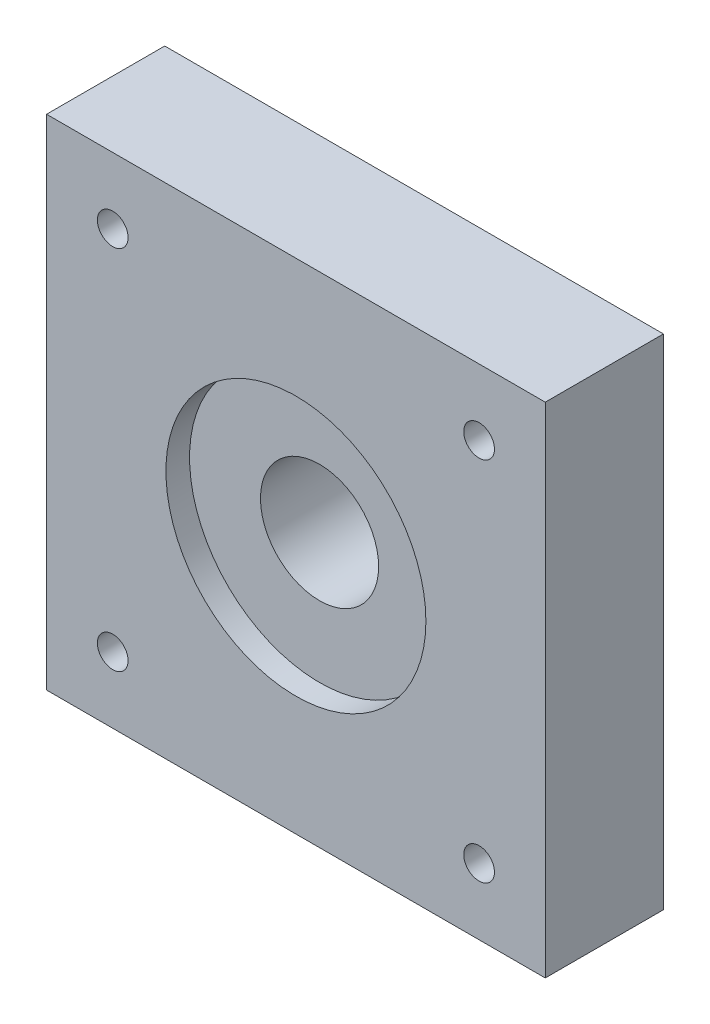
SolidWorks part; units mm, degrees
ref_plane "Front" through (0, 0, 0) normal (0, 0, 1) x (1, 0, 0)
ref_plane "Top" through (0, 0, 0) normal (0, 1, 0) x (1, 0, 0)
ref_plane "Right" through (0, 0, 0) normal (1, 0, 0) x (0, 0, -1)
sketch "草图1" plane through (0, 0, 0) normal (0, 0, 1) x (1, 0, 0)
  line L1 (-21.1, -21.1) -> (21.1, -21.1)
  line L2 (-21.1, -21.1) -> (-21.1, 21.1)
  line L3 (-21.1, 21.1) -> (21.1, 21.1)
  line L4 (21.1, -21.1) -> (21.1, 21.1)
  line L5 (-21.1, -21.1) -> (21.1, 21.1) construction
  line L6 (-21.1, 21.1) -> (21.1, -21.1) construction
  point P0 (0, 0)
  point P6 (11.6426, -11.7023)
  dimension "D2" = 42.2
extrude "凸台-拉伸1" add sketch "草图1" along normal blind 10
sketch "草图2" plane through (0, 0, 0) normal (0, 0, -1) x (-1, 0, 0)
  line L5 (-12.5, 0) -> (12.5, 0) construction
  line L6 (0, -12.5) -> (0, 12.5) construction
  circle A0 centre (12.5, 0) radius 1.6
  circle A1 centre (0, -12.5) radius 1.6
  circle A2 centre (-12.5, 0) radius 1.6
  circle A3 centre (0, 12.5) radius 1.6
  circle A4 centre (-15.5, 15.5) radius 3
  circle A5 centre (15.5, 15.5) radius 3
  circle A6 centre (15.5, -15.5) radius 3
  circle A7 centre (-15.5, -15.5) radius 3
  point P0 (0, 0)
  point P10 (0, 0)
  point P13 (0, 0)
  point P16 (0, 0)
  point P19 (0, 0)
  point P27 (0, 0)
  dimension "D2" = 3.2
  dimension "D1" = 25
  dimension "D4" = 4
  dimension "D3" = 4
extrude "切除-拉伸1" cut sketch "草图2" against normal blind 6
sketch "草图3" plane through (0, 0, 10) normal (0, 0, 1) x (1, 0, 0)
  circle A0 centre (0, 0) radius 11
extrude "切除-拉伸2" cut sketch "草图3" against normal blind 2
sketch "草图4" plane through (0, 0, 0) normal (0, 0, -1) x (-1, 0, 0)
  circle A0 centre (0, 0) radius 5
extrude "切除-拉伸3" cut sketch "草图4" against normal through all
sketch "草图5" plane through (0, 0, 10) normal (0, 0, 1) x (1, 0, 0)
  circle A0 centre (15.5, -15.5) radius 1.3
  circle A1 centre (-15.5, -15.5) radius 1.3
  circle A2 centre (-15.5, 15.5) radius 1.3
  circle A3 centre (15.5, 15.5) radius 1.3
  point P12 (0, 0)
  dimension "D1" = 4
extrude "切除-拉伸4" cut sketch "草图5" against normal through all
